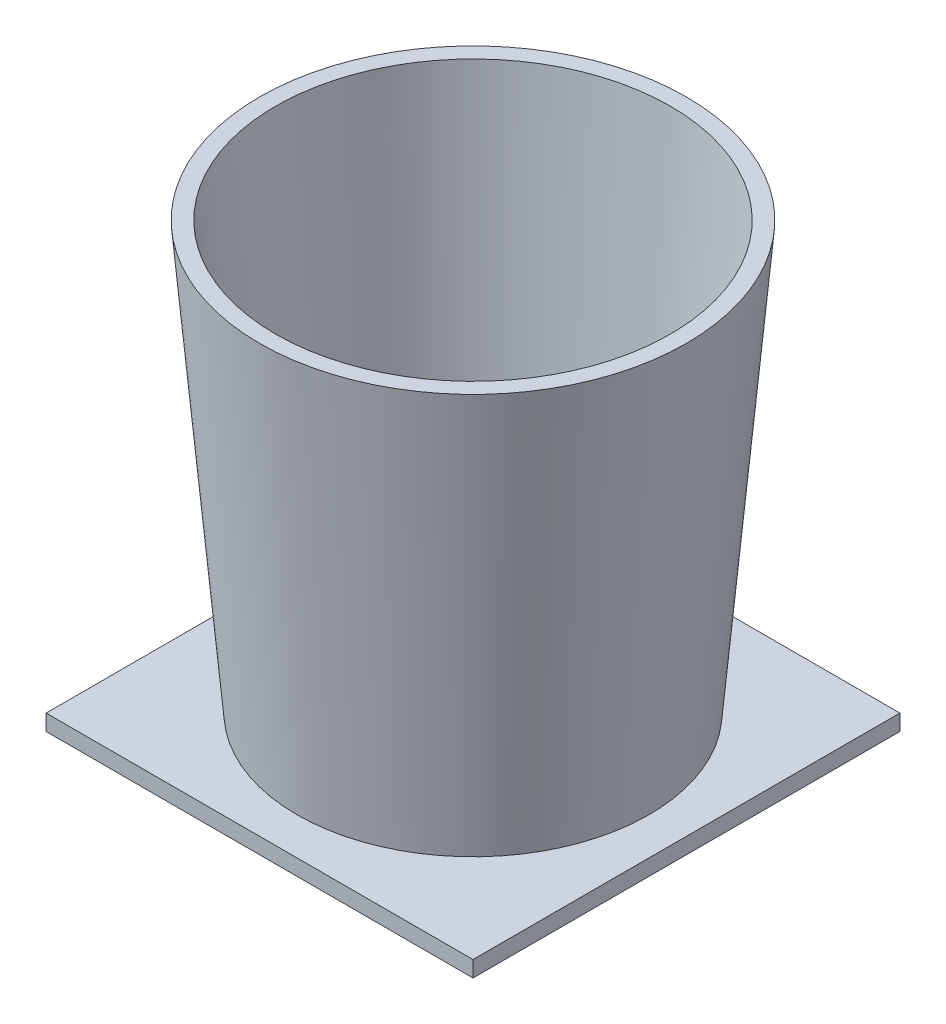
SolidWorks part; units mm, degrees
ref_plane "Plan de face" through (0, 0, 0) normal (0, 0, 1) x (1, 0, 0)
ref_plane "Plan de dessus" through (0, 0, 0) normal (0, 1, 0) x (1, 0, 0)
ref_plane "Plan de droite" through (0, 0, 0) normal (1, 0, 0) x (0, 0, -1)
sketch "Esquisse3" plane through (0, 0, 0) normal (0, 1, 0) x (1, 0, 0)
  line L1 (-40, 40) -> (40, 40)
  line L2 (-40, 40) -> (-40, -40)
  line L3 (-40, -40) -> (40, -40)
  line L4 (40, 40) -> (40, -40)
  dimension "D1" = 80
  dimension "D2" = 80
  dimension "D3" = 40
  dimension "D4" = 40
extrude "Boss.-Extru.1" add sketch "Esquisse3" along normal blind 3
sketch "Esquisse4" plane through (0, 0, 0) normal (0, 0, 1) x (1, 0, 0)
  line L0 (0, 5.328) -> (0, 25.2754) construction
  line L1 (33.0009, 3) -> (40, 83)
  line L2 (40, 83) -> (37, 83)
  line L3 (37, 83) -> (30.0009, 3)
  line L4 (30.0009, 3) -> (33.0009, 3)
  line L5 (-40, 3) -> (40, 3) construction
  dimension "D1" = 40
  dimension "D2" = 3
  dimension "D3" = 85
  dimension "D4" = 80
  dimension "D5" = 0
revolve "Révolution1" add sketch "Esquisse4" angle 360 about L0
